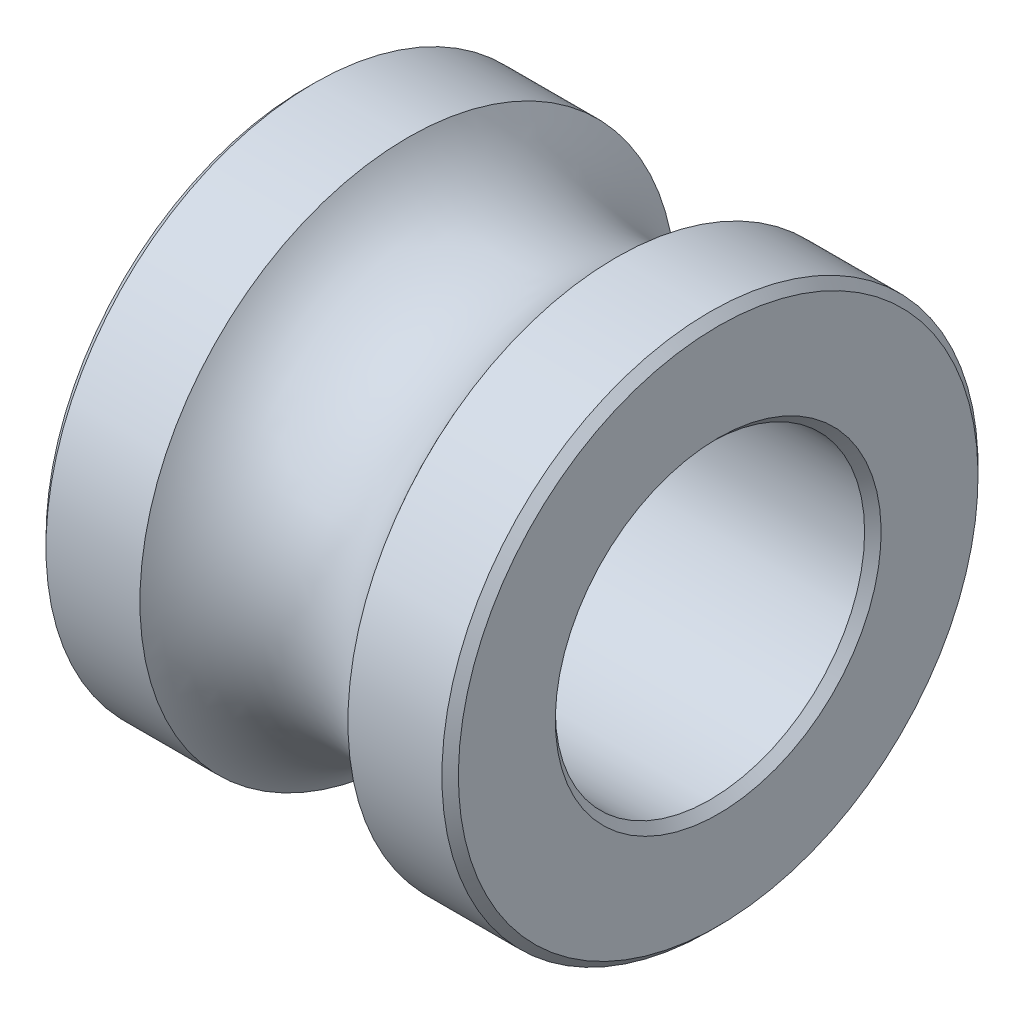
SolidWorks part; units mm, degrees
ref_plane "Front" through (0, 0, 0) normal (0, 0, 1) x (1, 0, 0)
ref_plane "Top" through (0, 0, 0) normal (0, 1, 0) x (1, 0, 0)
ref_plane "Right" through (0, 0, 0) normal (1, 0, 0) x (0, 0, -1)
sketch "Sketch1" plane through (0, 0, 0) normal (0, 0, 1) x (1, 0, 0)
  line L0 (-6.429, 0) -> (6.429, 0) construction
  line L1 (-2, -1.5) -> (2, -1.5) construction
  line L2 (-1.6, -4) -> (-0.9367, -4) construction
  line L3 (-2, -4) -> (-2, -5) construction
  line L4 (-2, -5) -> (2, -5) construction
  line L5 (2, -4) -> (2, -5) construction
  line L6 (0, -1.5) -> (0, -5) construction
  line L7 (-2, -2.6) -> (2, -2.6) construction
  line L8 (-1.6, -4) -> (-1.6, -4.1) construction
  line L9 (-1.6, -4.1) -> (-1.8, -4.1) construction
  line L10 (-1.8, -4.1) -> (-1.8, -4) construction
  line L11 (-1.8, -4) -> (-2, -4) construction
  line L12 (1.8, -4) -> (2, -4) construction
  line L13 (1.8, -4.1) -> (1.8, -4) construction
  line L14 (1.6, -4.1) -> (1.8, -4.1) construction
  line L15 (1.6, -4) -> (1.6, -4.1) construction
  line L16 (0.9367, -4) -> (1.6, -4) construction
  line L17 (-2, -1.5) -> (-2, -2.6)
  line L18 (-2, -2.6) -> (-1.0087, -2.6)
  line L19 (-2, -1.5) -> (2, -1.5)
  line L20 (2, -1.5) -> (2, -2.6)
  line L21 (2, -2.6) -> (1.0087, -2.6)
  circle A0 centre (0, -3.25) radius 1.2 construction
  arc A1 (-1.0087, -2.6) -> (1.0087, -2.6) centre (0, -3.25) cw
  point P13 (0, -3.25)
  point P15 (-1.8, -4.05)
  point P26 (0, 0)
  point P28 (-1.0087, -2.6)
  point P30 (0, -2.6)
  dimension "D3" = 2.4
  dimension "D1" = 5
  dimension "D2" = 1.5
  dimension "D4" = 2.6
  dimension "D5" = 4
  dimension "D6" = 0.4
  dimension "D7" = 4
  dimension "D8" = 0.1
  dimension "D9" = 0.2
  dimension "D11" = 4
revolve "Revolve1" add sketch "Sketch1" angle 360 about L0
chamfer "Chamfer1" distance 0.08 angle 45 4 edges at (-2, -1.5, 0) (-2, -2.6, 0) (2, -2.6, 0) (2, -1.5, 0)
